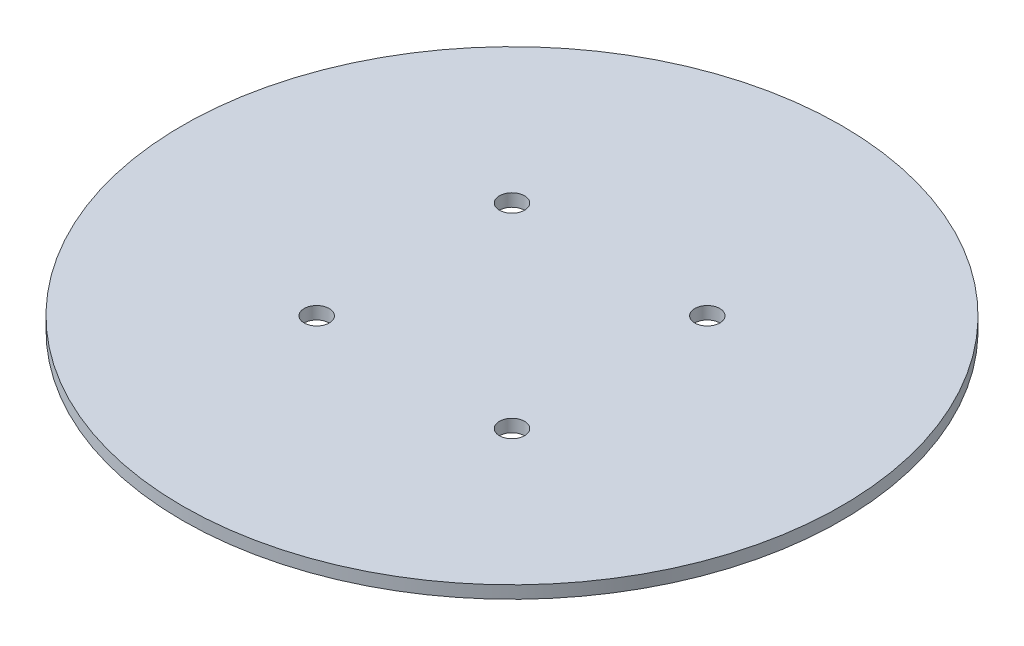
SolidWorks part; units mm, degrees
ref_plane "Plano frontal" through (0, 0, 0) normal (0, 0, 1) x (1, 0, 0)
ref_plane "Plano superior" through (0, 0, 0) normal (0, 1, 0) x (1, 0, 0)
ref_plane "Plano direito" through (0, 0, 0) normal (1, 0, 0) x (0, 0, -1)
sketch "Esboço1" plane through (0, 0, 0) normal (0, 1, 0) x (1, 0, 0)
  circle A0 centre (0, 0) radius 105
  dimension "D1" = 210
extrude "Ressalto-extrusão1" add sketch "Esboço1" along normal blind 4
sketch "Esboço4" plane through (0, 4, 0) normal (0, 1, 0) x (1, 0, 0)
  line L0 (-91.0375, -91.0375) -> (93.3433, 93.3433) construction
  line L1 (-94.4904, 94.4904) -> (110.9508, -110.9508) construction
  line L2 (-2.2, 0) -> (2.2, 0) construction
  circle A0 centre (0, 0) radius 44
  point P9 (31.1127, 31.1127)
  point P10 (-31.1127, 31.1127)
  point P11 (-31.1127, -31.1127)
  point P12 (31.1127, -31.1127)
  dimension "D1" = 45
  dimension "D2" = 45
sketch "Esboço5" plane through (0, 4, 0) normal (0, 1, 0) x (1, 0, 0)
  circle A0 centre (31.1127, -31.1127) radius 4
  circle A1 centre (31.1127, 31.1127) radius 4
  circle A2 centre (-31.1127, 31.1127) radius 4
  circle A3 centre (-31.1127, -31.1127) radius 4
extrude "Corte-extrusão1" cut sketch "Esboço5" against normal blind 10
